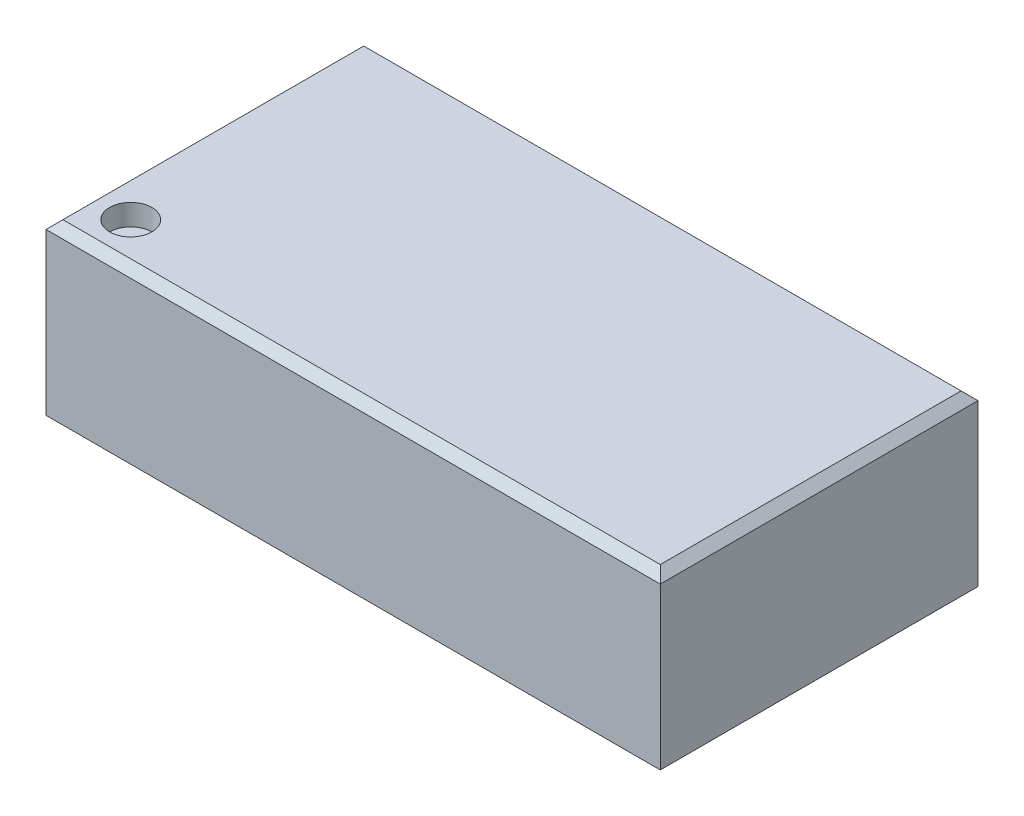
SolidWorks part; units mm, degrees
ref_plane "Plan de face" through (0, 0, 0) normal (0, 0, 1) x (1, 0, 0)
ref_plane "Plan de dessus" through (0, 0, 0) normal (0, 1, 0) x (1, 0, 0)
ref_plane "Plan de droite" through (0, 0, 0) normal (1, 0, 0) x (0, 0, -1)
sketch "Esquisse1" plane through (0, 0, 0) normal (0, 1, 0) x (1, 0, 0)
  line L0 (-6.2355, 0) -> (6.0843, 0) construction
  line L1 (0, 4.4782) -> (0, -3.2689) construction
  line L3 (-3.625, 1.875) -> (3.625, 1.875)
  line L4 (-3.625, 1.875) -> (-3.625, -1.875)
  line L5 (-3.625, -1.875) -> (3.625, -1.875)
  line L6 (3.625, 1.875) -> (3.625, -1.875)
  dimension "D1" = 7.25
  dimension "D2" = 3.75
extrude "Boss.-Extru.1" add sketch "Esquisse1" along normal blind 2
sketch "Esquisse2" plane through (0, 2, 0) normal (0, 1, 0) x (1, 0, 0)
  line L0 (-3.625, -1.875) -> (3.625, -1.875) construction
  line L1 (-3.625, 1.875) -> (-3.625, -1.875) construction
  circle A0 centre (-3.125, -1.375) radius 0.25
  dimension "D1" = 0.5
  dimension "D2" = 0.5
  dimension "D3" = 0.5
extrude "Enlèv. mat.-Extru.1" cut sketch "Esquisse2" against normal blind 0.25
chamfer "Chanfrein1" distance 0.1 angle 45 4 edges at (3.625, 2, 0) (0, 2, 1.875) (0, 2, -1.875) (-3.625, 2, 0)
